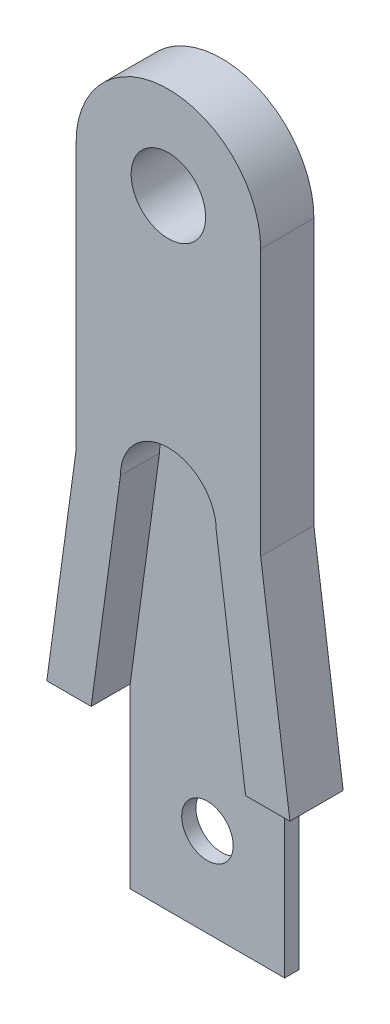
SolidWorks part; units mm, degrees
ref_plane "Front Plane" through (0, 0, 0) normal (0, 0, 1) x (1, 0, 0)
ref_plane "Top Plane" through (0, 0, 0) normal (0, 1, 0) x (1, 0, 0)
ref_plane "Right Plane" through (0, 0, 0) normal (1, 0, 0) x (0, 0, -1)
ref_plane "Plane1" through (0, 0, 4.0561) normal (0, 0, -1) x (-1, 0, 0)
sketch "Sketch1" plane through (0, 0, 4.0561) normal (0, 0, -1) x (-1, 0, 0)
  line L0 (-1.9417, 16.5118) -> (-3.5917, 4.4118)
  line L1 (-3.5917, 4.4118) -> (10.1083, 4.4118)
  line L2 (10.1083, 4.4118) -> (8.4583, 16.5118)
  line L3 (8.4583, 16.5118) -> (8.4583, 31.5118)
  line L4 (-1.9417, 31.5118) -> (-1.9417, 16.5118)
  arc A0 (8.4583, 31.5118) -> (-1.9417, 31.5118) centre (3.2583, 31.5118) ccw
  dimension "D1" = 13.7
extrude "Boss-Extrude1" add sketch "Sketch1" against normal blind 3
sketch "Sketch2" plane through (0, 0, 7.0561) normal (0, 0, 1) x (1, 0, 0)
  line L0 (1.0917, 4.4118) -> (-0.5583, 16.5118)
  line L1 (-5.9583, 16.5118) -> (-7.6083, 4.4118)
  line L2 (-7.6083, 4.4118) -> (1.0917, 4.4118)
  arc A0 (-0.5583, 16.5118) -> (-5.9583, 16.5118) centre (-3.2583, 16.5118) ccw
extrude "Cut-Extrude1" cut sketch "Sketch2" against normal blind 2.2
sketch "Sketch3" plane through (0, 4.4118, 0) normal (0, -1, 0) x (1, 0, 0)
  line L0 (1.0917, 4.0561) -> (-7.6083, 4.0561)
  line L1 (-7.6083, 4.0561) -> (-7.6083, 4.8561)
  line L2 (-7.6083, 4.8561) -> (1.0917, 4.8561)
  line L3 (1.0917, 4.8561) -> (1.0917, 4.0561)
extrude "Boss-Extrude2" add sketch "Sketch3" along normal blind 10
hole_wizard "Ø3.7 (3.7) Diameter Hole1" positions "Sketch5" profile "Sketch4" hole size "Ø3.7" standard "ANSI Metric" end condition through all
sketch "Sketch5" plane through (0, 0, 4.0561) normal (0, 0, -1) x (-1, 0, 0)
  point P0 (3.2583, 31.5118)
sketch "Sketch4" plane through (-3.2583, 31.5118, 4.0561) normal (1, 0, 0) x (0, 1, 0)
  line L0 (0, 0) -> (0, 3)
  line L1 (0, 3) -> (2.1, 3)
  line L2 (2.1, 3) -> (2.1, 0)
  line L5 (2.1, 0) -> (0, 0)
  line L11 (0, -6.35) -> (0, 107.95) construction
  dimension "Thru Hole Dia." = 4.2
  dimension "Thru Hole Depth" = 3
hole_wizard "Ø2.9 (2.9) Diameter Hole1" positions "Sketch7" profile "Sketch6" hole size "Ø2.9" standard "ANSI Metric" end condition through all
sketch "Sketch7" plane through (0, 0, 4.0561) normal (0, 0, -1) x (-1, 0, 0)
  point P0 (3.2583, -0.5882)
sketch "Sketch6" plane through (-3.2583, -0.5882, 4.0561) normal (1, 0, 0) x (0, 1, 0)
  line L0 (0, 0) -> (0, 3)
  line L1 (0, 3) -> (1.45, 3)
  line L2 (1.45, 3) -> (1.45, 0)
  line L5 (1.45, 0) -> (0, 0)
  line L11 (0, -6.35) -> (0, 107.95) construction
  dimension "Thru Hole Dia." = 2.9
  dimension "Thru Hole Depth" = 3
